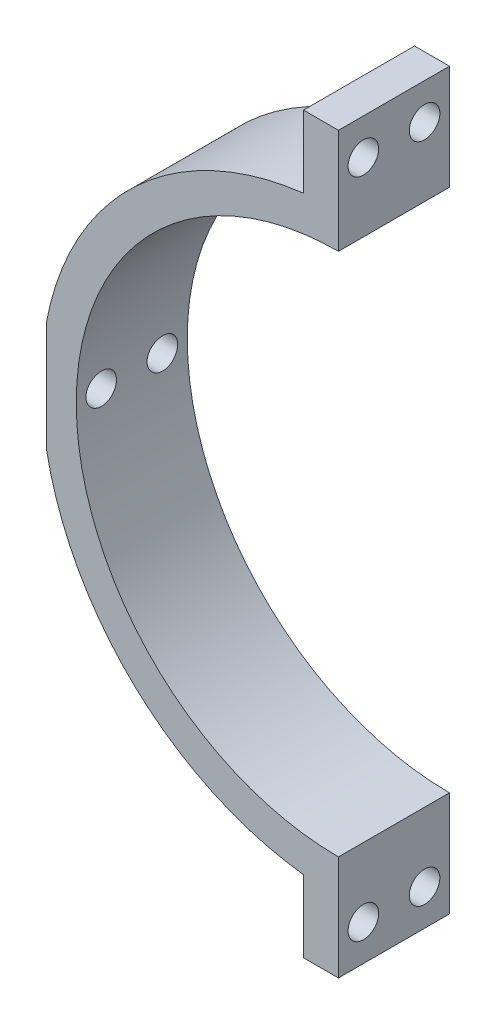
SolidWorks part; units mm, degrees
ref_plane "Alzado" through (0, 0, 0) normal (0, 0, 1) x (1, 0, 0)
ref_plane "Planta" through (0, 0, 0) normal (0, 1, 0) x (1, 0, 0)
ref_plane "Vista lateral" through (0, 0, 0) normal (1, 0, 0) x (0, 0, -1)
sketch "Croquis1" plane through (0, 0, 0) normal (0, 0, 1) x (1, 0, 0)
  line L0 (0, 42) -> (0, -42)
  line L1 (0, 42) -> (-4, 42)
  line L2 (-4, 42) -> (-4, 33.7639)
  line L3 (-4, -42) -> (0, -42)
  line L4 (-4, -33.7639) -> (-4, -42)
  line L6 (-34.5982, -6.35) -> (-33.4018, -6.35)
  line L7 (-34.5982, -6.35) -> (-34.5982, 6.35)
  line L8 (-34.5982, 6.35) -> (-33.4018, 6.35)
  line L9 (-33.4018, -6.35) -> (-33.4018, 6.35)
  line L10 (-34.5982, -6.35) -> (-33.4018, 6.35) construction
  line L11 (-34.5982, 6.35) -> (-33.4018, -6.35) construction
  arc A0 (0, 30) -> (0, -30) centre (0, 0) ccw
  arc A1 (-4, 33.7639) -> (-4, -33.7639) centre (0, 0) ccw
  point P6 (-34, 0)
  point P15 (-33.4018, 6.35)
  dimension "D1" = 60
  dimension "D2" = 68
  dimension "D3" = 84
  dimension "D4" = 42
  dimension "D5" = 4
  dimension "D6" = 12.7
extrude "Saliente-Extruir1" add sketch "Croquis1" along normal blind 12.7 contours L2 A1 L4 L3 L0 A0 L1
sketch "Croquis2" plane through (-4, 0, 0) normal (-1, 0, 0) x (0, 0, 1)
  line L0 (0, 37.8819) -> (12.7, 37.8819) construction
  line L1 (0, 42) -> (0, 33.7639) construction
  line L2 (12.7, 42) -> (12.7, 33.7639) construction
  circle A0 centre (2.85, 37.8819) radius 1.75
  circle A1 centre (9.85, 37.8819) radius 1.75
  point P10 (6.35, 37.8819)
  dimension "D1" = 3.5
  dimension "D2" = 3.5
  dimension "D3" = 3.5
  dimension "D4" = 3.5
extrude "Cortar-Extruir1" cut sketch "Croquis2" against normal up to next (4 mm away)
mirror "Simetría1" about plane through (0, 0, 0) normal (0, 1, 0) of "Cortar-Extruir1"
sketch "Croquis3" plane through (-33.4018, 0, 0) normal (-1, 0, 0) x (0, 0, 1)
  line L0 (0, 0) -> (12.7, 0) construction
  line L1 (12.7, -6.35) -> (12.7, 6.35) construction
  circle A0 centre (2.85, 0) radius 1.75
  circle A1 centre (9.85, 0) radius 1.75
  point P9 (6.35, 0)
  dimension "D1" = 3.5
  dimension "D2" = 3.5
  dimension "D3" = 3.5
  dimension "D4" = 3.5
extrude "Cortar-Extruir2" cut sketch "Croquis3" against normal up to next
